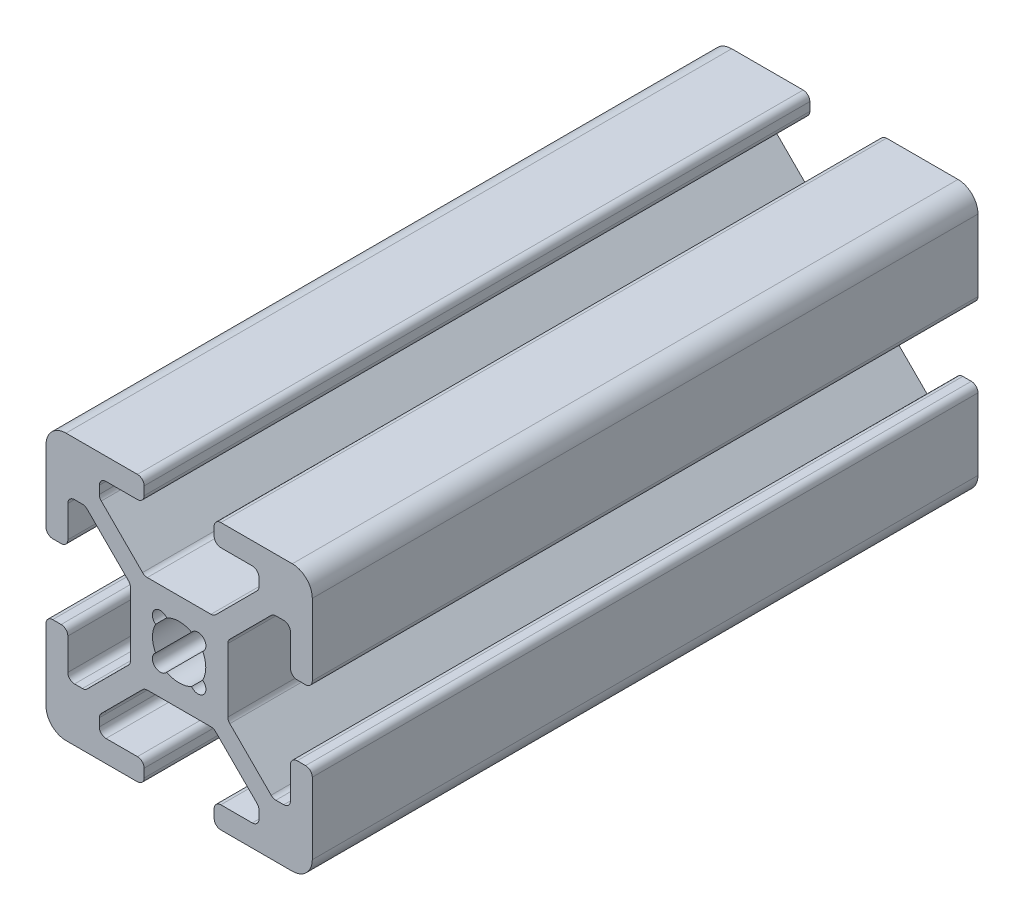
SolidWorks part; units mm, degrees
ref_plane "Front Plane" through (0, 0, 0) normal (0, 0, 1) x (1, 0, 0)
ref_plane "Top Plane" through (0, 0, 0) normal (0, 1, 0) x (1, 0, 0)
ref_plane "Right Plane" through (0, 0, 0) normal (1, 0, 0) x (0, 0, -1)
sketch "Sketch1" plane through (0, 0, 0) normal (0, 0, 1) x (1, 0, 0)
  line L0 (-2.7464, -3.807) -> (-5.848, -6.9086)
  line L1 (-8.5, -10) -> (-3.1319, -10)
  line L2 (-10, -8.5) -> (-10, -3.1319)
  line L3 (-8.5, 10) -> (-3.1319, 10)
  line L4 (10, -8.5) -> (10, -3.1319)
  line L6 (-10, 10) -> (-8.36, 8.36) construction
  line L7 (-2.3914, -3.66) -> (2.3914, -3.66)
  line L8 (-3.66, -2.3914) -> (-3.66, 2.3914)
  line L9 (-2.3914, 3.66) -> (2.3914, 3.66)
  line L10 (3.66, -2.3914) -> (3.66, 2.3914)
  line L13 (-5.4931, -8.36) -> (-3.1319, -8.36)
  line L14 (2.7464, -3.807) -> (5.848, -6.9086)
  line L15 (3.807, -2.7464) -> (6.9086, -5.848)
  line L16 (-5.995, -14.365) -> (5.995, -14.365)
  line L17 (2.63, -9.4981) -> (2.63, -8.8619)
  line L18 (8.8619, -2.63) -> (9.4981, -2.63)
  line L19 (5.995, -7.8581) -> (5.995, -7.2636)
  line L20 (-10, 3.1319) -> (-10, 8.5)
  line L22 (7.2636, -5.995) -> (7.8581, -5.995)
  line L23 (8.36, -5.4931) -> (8.36, -3.1319)
  line L24 (-3.807, -2.7464) -> (-6.9086, -5.848)
  line L25 (-9.4981, -2.63) -> (-8.8619, -2.63)
  line L26 (-7.8581, -5.995) -> (-7.2636, -5.995)
  line L27 (-5.995, -7.2636) -> (-5.995, -7.8581)
  line L28 (-2.63, -8.8619) -> (-2.63, -9.4981)
  line L30 (-5.4931, -8.36) -> (-3.1319, -8.36)
  line L31 (-3.807, 2.7464) -> (-6.9086, 5.848)
  line L32 (-2.7464, 3.807) -> (-5.848, 6.9086)
  line L33 (-2.63, 9.4981) -> (-2.63, 8.8619)
  line L34 (-5.995, 7.8581) -> (-5.995, 7.2636)
  line L35 (-7.2636, 5.995) -> (-7.8581, 5.995)
  line L36 (-8.8619, 2.63) -> (-9.4981, 2.63)
  line L37 (3.1319, 10) -> (8.5, 10)
  line L38 (-8.36, 5.4931) -> (-8.36, 3.1319)
  line L39 (2.7464, 3.807) -> (5.848, 6.9086)
  line L40 (3.807, 2.7464) -> (6.9086, 5.848)
  line L41 (9.4981, 2.63) -> (8.8619, 2.63)
  line L42 (7.8581, 5.995) -> (7.2636, 5.995)
  line L43 (5.995, 7.2636) -> (5.995, 7.8581)
  line L44 (2.63, 8.8619) -> (2.63, 9.4981)
  line L45 (8.36, -5.4931) -> (8.36, -3.1319)
  line L46 (5.4931, 8.36) -> (3.1319, 8.36)
  line L49 (-8.36, 5.4931) -> (-8.36, 3.1319)
  line L50 (5.4931, 8.36) -> (3.1319, 8.36)
  line L51 (-3.1319, 8.36) -> (-5.4931, 8.36)
  line L52 (-3.1319, 8.36) -> (-5.4931, 8.36)
  line L53 (10, 8.36) -> (8.36, 8.36) [skipped]
  line L54 (10, 3.1319) -> (10, 8.5)
  line L55 (8.36, 3.1319) -> (8.36, 5.4931)
  line L56 (8.36, 3.1319) -> (8.36, 5.4931)
  line L57 (3.1319, -8.36) -> (5.4931, -8.36)
  line L58 (3.1319, -8.36) -> (5.4931, -8.36)
  line L59 (3.1319, -10) -> (8.5, -10)
  line L60 (-8.36, -3.1319) -> (-8.36, -5.4931)
  line L61 (-8.36, -3.1319) -> (-8.36, -5.4931)
  line L62 (-8.36, 10) -> (-8.36, 8.36) [skipped]
  arc A0 (-8.5, -10) -> (-10, -8.5) centre (-8.5, -8.5) cw
  arc A1 (8.5, -10) -> (10, -8.5) centre (8.5, -8.5) ccw
  arc A2 (10, 8.5) -> (8.5, 10) centre (8.5, 8.5) ccw
  arc A3 (-8.5, 10) -> (-10, 8.5) centre (-8.5, 8.5) ccw
  arc A4 (10, -3.1319) -> (9.4981, -2.63) centre (9.4981, -3.1319) ccw
  arc A5 (8.8619, -2.63) -> (8.36, -3.1319) centre (8.8619, -3.1319) ccw
  arc A6 (7.8581, -5.995) -> (8.36, -5.4931) centre (7.8581, -5.4931) ccw
  arc A7 (7.2636, -5.995) -> (6.9086, -5.848) centre (7.2636, -5.4931) cw
  arc A8 (5.995, -7.2636) -> (5.848, -6.9086) centre (5.4931, -7.2636) ccw
  arc A9 (5.995, -7.8581) -> (5.4931, -8.36) centre (5.4931, -7.8581) cw
  arc A10 (3.1319, -10) -> (2.63, -9.4981) centre (3.1319, -9.4981) cw
  arc A11 (2.63, -8.8619) -> (3.1319, -8.36) centre (3.1319, -8.8619) cw
  arc A12 (-3.1319, -10) -> (-2.63, -9.4981) centre (-3.1319, -9.4981) ccw
  arc A13 (-2.63, -8.8619) -> (-3.1319, -8.36) centre (-3.1319, -8.8619) ccw
  arc A14 (-5.4931, -8.36) -> (-5.995, -7.8581) centre (-5.4931, -7.8581) cw
  arc A15 (-5.995, -7.2636) -> (-5.848, -6.9086) centre (-5.4931, -7.2636) cw
  arc A16 (-9.4981, -2.63) -> (-10, -3.1319) centre (-9.4981, -3.1319) ccw
  arc A17 (-8.36, -3.1319) -> (-8.8619, -2.63) centre (-8.8619, -3.1319) ccw
  arc A18 (-7.2636, -5.995) -> (-6.9086, -5.848) centre (-7.2636, -5.4931) ccw
  arc A19 (-7.8581, -5.995) -> (-8.36, -5.4931) centre (-7.8581, -5.4931) cw
  arc A20 (-3.807, -2.7464) -> (-3.66, -2.3914) centre (-4.1619, -2.3914) ccw
  arc A21 (-2.3914, -3.66) -> (-2.7464, -3.807) centre (-2.3914, -4.1619) ccw
  arc A22 (2.7464, -3.807) -> (2.3914, -3.66) centre (2.3914, -4.1619) ccw
  arc A23 (3.807, -2.7464) -> (3.66, -2.3914) centre (4.1619, -2.3914) cw
  arc A24 (9.4981, 2.63) -> (10, 3.1319) centre (9.4981, 3.1319) ccw
  arc A25 (8.8619, 2.63) -> (8.36, 3.1319) centre (8.8619, 3.1319) cw
  arc A26 (5.848, 6.9086) -> (5.995, 7.2636) centre (5.4931, 7.2636) ccw
  arc A27 (7.2636, 5.995) -> (6.9086, 5.848) centre (7.2636, 5.4931) ccw
  arc A28 (8.36, 5.4931) -> (7.8581, 5.995) centre (7.8581, 5.4931) ccw
  arc A29 (5.995, 7.8581) -> (5.4931, 8.36) centre (5.4931, 7.8581) ccw
  arc A30 (3.66, 2.3914) -> (3.807, 2.7464) centre (4.1619, 2.3914) cw
  arc A31 (-3.66, 2.3914) -> (-3.807, 2.7464) centre (-4.1619, 2.3914) ccw
  arc A32 (2.3914, 3.66) -> (2.7464, 3.807) centre (2.3914, 4.1619) ccw
  arc A33 (-2.3914, 3.66) -> (-2.7464, 3.807) centre (-2.3914, 4.1619) cw
  arc A34 (3.1319, 8.36) -> (2.63, 8.8619) centre (3.1319, 8.8619) cw
  arc A35 (2.63, 9.4981) -> (3.1319, 10) centre (3.1319, 9.4981) cw
  arc A36 (-9.4981, 2.63) -> (-10, 3.1319) centre (-9.4981, 3.1319) cw
  arc A37 (-8.8619, 2.63) -> (-8.36, 3.1319) centre (-8.8619, 3.1319) ccw
  arc A38 (-3.1319, 8.36) -> (-2.63, 8.8619) centre (-3.1319, 8.8619) ccw
  arc A39 (-2.63, 9.4981) -> (-3.1319, 10) centre (-3.1319, 9.4981) ccw
  arc A40 (-5.848, 6.9086) -> (-5.995, 7.2636) centre (-5.4931, 7.2636) cw
  arc A41 (-5.4931, 8.36) -> (-5.995, 7.8581) centre (-5.4931, 7.8581) ccw
  arc A42 (-6.9086, 5.848) -> (-7.2636, 5.995) centre (-7.2636, 5.4931) ccw
  arc A43 (-7.8581, 5.995) -> (-8.36, 5.4931) centre (-7.8581, 5.4931) ccw
  arc A44 (-1.7677, 0.9356) -> (-1.7677, -0.9356) centre (0, 0) ccw
  arc A45 (-0.9356, 1.7677) -> (-1.7677, 0.9356) centre (-1.4142, 1.4142) ccw
  arc A46 (1.7677, 0.9356) -> (0.9356, 1.7677) centre (1.4142, 1.4142) ccw
  arc A47 (0.9356, -1.7677) -> (1.7677, -0.9356) centre (1.4142, -1.4142) ccw
  arc A48 (-1.7677, -0.9356) -> (-0.9356, -1.7677) centre (-1.4142, -1.4142) ccw
  arc A49 (-0.9356, -1.7677) -> (0.9356, -1.7677) centre (0, 0) ccw
  arc A50 (1.7677, -0.9356) -> (1.7677, 0.9356) centre (0, 0) ccw
  arc A51 (0.9356, 1.7677) -> (-0.9356, 1.7677) centre (0, 0) ccw
  point P0 (0, 0)
  point P5 (0, 0)
  point P9 (-10, -10)
  point P11 (0, -10)
  point P14 (0, -3.66)
  point P23 (3.66, 0)
  point P66 (0, 0)
  point P70 (0, 0)
  dimension "D2" = 1.5
  dimension "D5" = 0.5019
  dimension "D6" = 4
  dimension "D7" = 1.19
  dimension "D1" = 20
  dimension "D3" = 11.99
  dimension "D4" = 4
  dimension "D8" = 4
extrude "Boss-Extrude1" add sketch "Sketch1" along normal blind 50 contours A43 L35 A42 L31 A31 L8 A20 L24 A18 L26 A19 L60 A17 L25 A16 L2 A0 L1 A12 L28 A13 L13 A14 L27 A15 L0 A21 L7 A22 L14 A8 L19 A9 L57 A11 L17 A10 L59 A1 L4 A4 L18 A5 L23 A6 L22 A7 L15 A23 L10 A30
